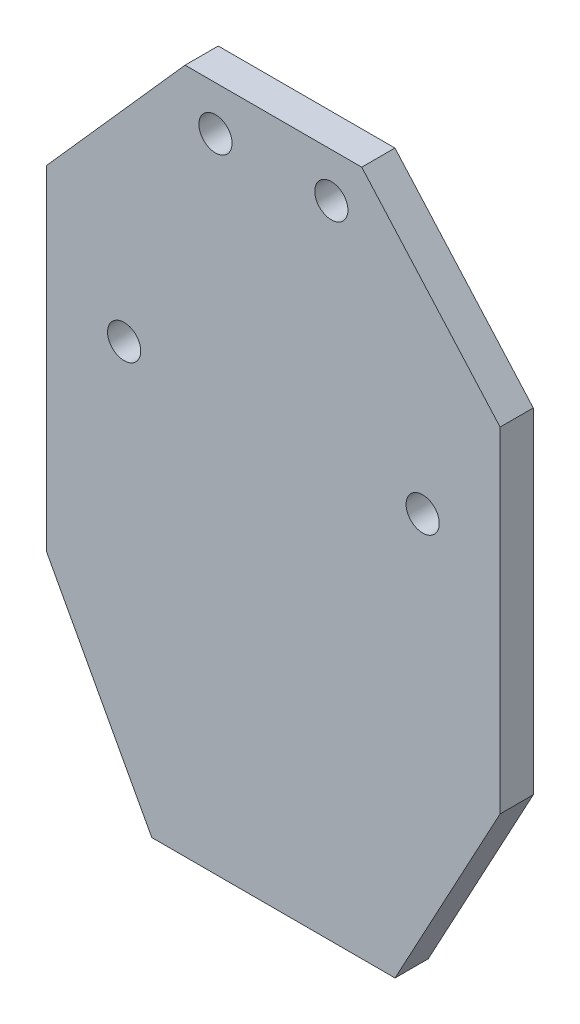
SolidWorks part; units mm, degrees
ref_plane "前视基准面" through (0, 0, 0) normal (0, 0, 1) x (1, 0, 0)
ref_plane "上视基准面" through (0, 0, 0) normal (0, 1, 0) x (1, 0, 0)
ref_plane "右视基准面" through (0, 0, 0) normal (1, 0, 0) x (0, 0, -1)
other "Configuration Table"
sketch "草图1" plane through (0, 0, 0) normal (0, 0, 1) x (1, 0, 0)
  line L0 (0, 0) -> (0, 62) construction
  line L1 (11, 0) -> (-11, 0)
  line L2 (-11, 0) -> (-20.5, 17.5997)
  line L3 (-20.5, 17.5997) -> (-20.5, 47.8997)
  line L4 (-20.5, 47.8997) -> (-7.9898, 62)
  line L5 (-7.9898, 62) -> (7.9898, 62)
  line L6 (20.5, 47.8997) -> (7.9898, 62)
  line L7 (20.5, 17.5997) -> (20.5, 47.8997)
  line L8 (11, 0) -> (20.5, 17.5997)
  line L10 (-13.5, 37.5997) -> (-12, 37.5997) construction
  line L11 (11.2547, 30.1152) -> (7.5, 17.5997) construction
  line L19 (8.4907, 37.5997) -> (8.7206, 37.5997) construction
  line L20 (12, 37.5997) -> (13.5, 37.5997) construction
  line L21 (-8.7206, 37.5997) -> (-8.4907, 37.5997) construction
  circle A0 centre (-5.2398, 58) radius 1.5
  circle A1 centre (-13.5, 37.5997) radius 1.5
  circle A4 centre (13.5, 37.5997) radius 1.5
  circle A5 centre (5.2398, 58) radius 1.5
  arc A7 (-12.5706, 42.522) -> (-12.5706, 32.6774) centre (-13.5, 37.5997) ccw construction
  dimension "D2" = 3
  dimension "D10" = 4
  dimension "D1" = 62
  dimension "D4" = 11
  dimension "D5" = 20
  dimension "D6" = 30.3
  dimension "D7" = 7
  dimension "D8" = 10.3
  dimension "D9" = 2.75
  dimension "D11" = 18.85
  dimension "D12" = 20.5
  dimension "D14" = 13
extrude "凸台-拉伸1" add sketch "草图1" along normal blind 3
